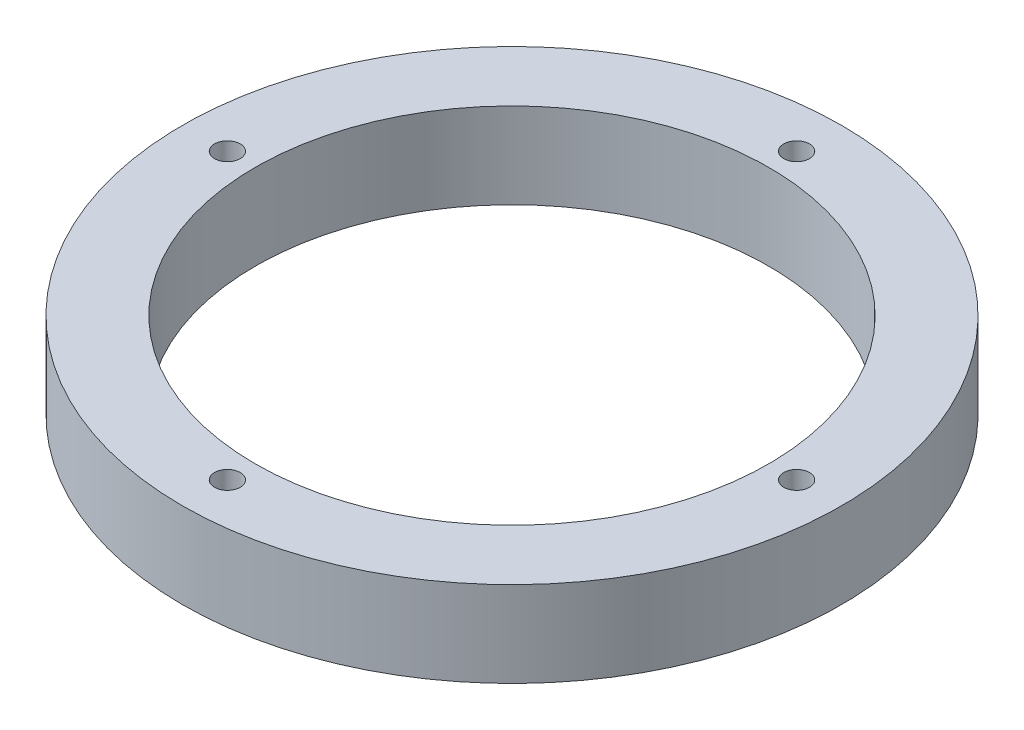
SolidWorks part; units mm, degrees
ref_plane "Front Plane" through (0, 0, 0) normal (0, 0, 1) x (1, 0, 0)
ref_plane "Top Plane" through (0, 0, 0) normal (0, 1, 0) x (1, 0, 0)
ref_plane "Right Plane" through (0, 0, 0) normal (1, 0, 0) x (0, 0, -1)
sketch "Sketch1" plane through (0, 0, 0) normal (0, 1, 0) x (1, 0, 0)
  line L0 (0, 0) -> (0, 48.895) construction
  circle A0 centre (0, 0) radius 48.895
  circle A1 centre (0, 0) radius 38.1
  circle A2 centre (0, 42.2275) radius 1.905
  circle A3 centre (42.2275, 0) radius 1.905
  circle A4 centre (0, -42.2275) radius 1.905
  circle A5 centre (-42.2275, 0) radius 1.905
  point P18 (0, 0)
  dimension "D1" = 42.2275
  dimension "D2" = 4
extrude "Boss-Extrude1" add sketch "Sketch1" along normal blind 12.7
